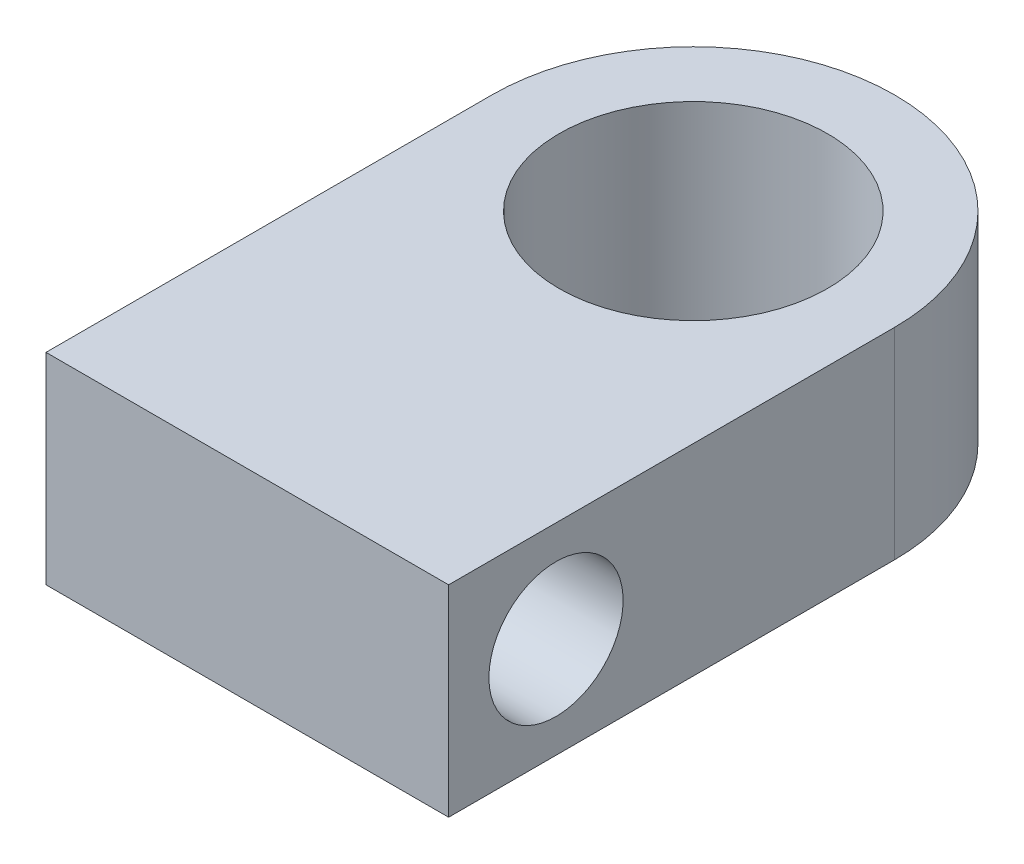
SolidWorks part; units mm, degrees
ref_plane "Front Plane" through (0, 0, 0) normal (0, 0, 1) x (1, 0, 0)
ref_plane "Top Plane" through (0, 0, 0) normal (0, 1, 0) x (1, 0, 0)
ref_plane "Right Plane" through (0, 0, 0) normal (1, 0, 0) x (0, 0, -1)
sketch "Sketch1" plane through (0, 0, 0) normal (0, 1, 0) x (1, 0, 0)
  circle A0 centre (0, 0) radius 6.35
  circle A1 centre (0, 0) radius 9.525
  dimension "D1" = 12.7
  dimension "D2" = 19.05
extrude "Boss-Extrude1" add sketch "Sketch1" along normal blind 9.525
sketch "Sketch2" plane through (0, 9.525, 0) normal (0, 1, 0) x (1, 0, 0)
  line L0 (-9.525, 0) -> (-9.525, -21.1003)
  line L1 (-9.525, -21.1003) -> (9.525, -21.1003)
  line L2 (9.525, -21.1003) -> (9.525, 0)
  circle A0 centre (0, 0) radius 9.525 construction
  arc A1 (-9.525, 0) -> (9.525, 0) centre (0, 0) ccw
  dimension "D2" = 21.1003
  dimension "D1" = 19.05
extrude "Boss-Extrude2" add sketch "Sketch2" against normal through all
sketch "Sketch3" plane through (-9.525, 0, 0) normal (-1, 0, 0) x (0, 0, 1)
  line L0 (21.1003, 0) -> (21.1003, 9.525) construction
  circle A0 centre (16.0203, 4.7625) radius 3.175
  point P4 (21.1003, 4.7625)
  dimension "D1" = 6.35
  dimension "D2" = 5.08
extrude "Cut-Extrude1" cut sketch "Sketch3" against normal through all
